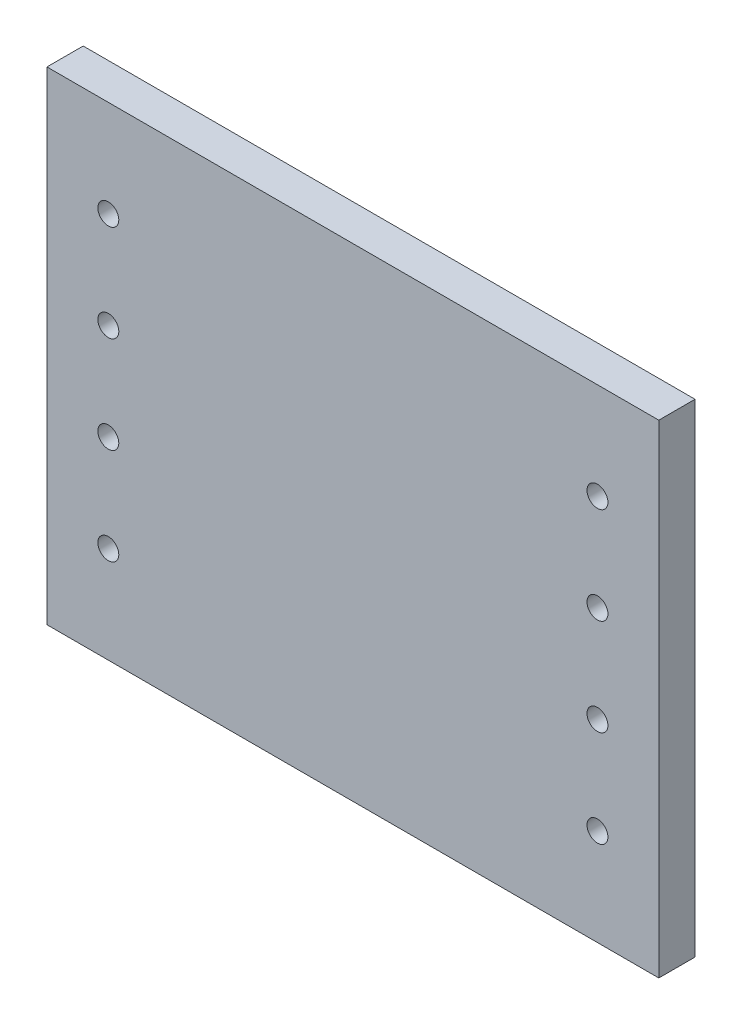
SolidWorks part; units mm, degrees
ref_plane "Front" through (0, 0, 0) normal (0, 0, 1) x (1, 0, 0)
ref_plane "Top" through (0, 0, 0) normal (0, 1, 0) x (1, 0, 0)
ref_plane "Right" through (0, 0, 0) normal (1, 0, 0) x (0, 0, -1)
sketch "Sketch1" plane through (0, 0, 0) normal (0, 0, 1) x (1, 0, 0)
  line L1 (23.481, 212.5625) -> (345.172, 212.5625)
  line L2 (345.172, 441.1625) -> (345.172, 237.9625) construction
  line L3 (23.481, 466.5625) -> (345.172, 466.5625)
  line L4 (345.172, 212.5625) -> (345.172, 466.5625)
  line L5 (345.172, 441.1625) -> (345.172, 237.9625) construction
  line L6 (23.481, 466.5625) -> (23.481, 212.5625)
  dimension "D2" = 254
extrude "Base-Extrude" add sketch "Sketch1" along normal blind 19.05
sketch "Sketch2" plane through (0, 0, 0) normal (0, 0, -1) x (-1, 0, 0)
  line L1 (-345.172, 466.5625) -> (-23.481, 466.5625) construction
  line L2 (-345.172, 466.5625) -> (-23.481, 466.5625) construction
  line L3 (-273.2265, 392.2739) -> (-273.2265, 245.7761)
  line L4 (-23.481, 212.5625) -> (-345.172, 212.5625) construction
  line L5 (-105.1421, 403.0625) -> (-263.511, 403.0625)
  line L6 (-105.1421, 403.0625) -> (-95.4265, 392.2739)
  line L7 (-263.511, 403.0625) -> (-273.2265, 392.2739)
  line L8 (-273.2265, 245.7761) -> (-95.4265, 245.7761)
  line L9 (-95.4265, 392.2739) -> (-95.4265, 245.7761)
  line L10 (-23.481, 212.5625) -> (-345.172, 212.5625) construction
  line L11 (-184.3265, 466.5625) -> (-184.3265, 212.5625) construction
  dimension "D1" = 177.8
extrude "Boss-Extrude1" add sketch "Sketch2" along normal blind 15.875
sketch "Sketch3" plane through (0, 0, -15.875) normal (0, 0, -1) x (-1, 0, 0)
  line L24 (-254.1765, 264.8261) -> (-114.4765, 264.8261)
  line L25 (-114.4765, 264.8261) -> (-114.4765, 384.0125)
  line L26 (-114.4765, 384.0125) -> (-254.1765, 384.0125)
  line L27 (-254.1765, 384.0125) -> (-254.1765, 264.8261)
  line L28 (-254.1765, 264.8261) -> (-114.4765, 264.8261)
  line L29 (-114.4765, 264.8261) -> (-114.4765, 384.0125)
  line L30 (-114.4765, 384.0125) -> (-254.1765, 384.0125)
  line L31 (-254.1765, 384.0125) -> (-254.1765, 264.8261)
  dimension "D2" = 19.05
extrude "Cut-Extrude1" cut sketch "Sketch3" against normal up to surface (15.875 mm away) up to face at (184.3265, 339.5625, 0)
fillet "Fillet3" radius 2.54 6 edges at (95.4265, 319.025, 0) (100.2843, 397.6682, 0) (184.3265, 403.0625, 0) (268.3688, 397.6682, 0) (273.2265, 319.025, 0) (184.3265, 245.7761, 0)
fillet "Fillet5" radius 6.35 4 edges at (254.1765, 264.8261, -7.9375) (114.4765, 264.8261, -7.9375) (114.4765, 384.0125, -7.9375) (254.1765, 384.0125, -7.9375)
fillet "Fillet6" radius 2.54 8 edges at (254.1765, 324.4193, 0) (184.3265, 384.0125, 0) (184.3265, 264.8261, 0) (114.4765, 324.4193, 0) (116.3364, 266.686, 0) (116.3364, 382.1526, 0) (252.3167, 266.686, 0) (252.3167, 382.1526, 0)
hole_wizard "CBORE for M10 SHCS1" positions "Sketch7" profile "Sketch6" counterbore size "M10" standard "Ansi Metric" end condition through all
sketch "Sketch7" plane through (0, 0, 0) normal (0, 0, -1) x (-1, 0, 0)
  line L0 (-345.172, 212.5625) -> (-345.172, 466.5625) construction
  line L1 (-345.172, 466.5625) -> (-23.481, 466.5625) construction
  point P0 (-312.914, 415.7625)
  dimension "D1" = 32.258
  dimension "D2" = 50.8
sketch "Sketch6" plane through (312.914, 415.7625, 0) normal (1, 0, 0) x (0, 1, 0)
  line L0 (0, 0) -> (0, 19.05)
  line L1 (0, 19.05) -> (5.5, 19.05)
  line L3 (5.5, 19.05) -> (5.5, 10)
  line L4 (5.5, 10) -> (9, 10)
  line L5 (9, 10) -> (9, 0)
  line L7 (9, 0) -> (0, 0)
  line L11 (0, -6.35) -> (0, 107.95) construction
  dimension "Thru Hole Dia." = 11
  dimension "Thru Hole Depth" = 19.05
  dimension "C'Bore Dia." = 18
  dimension "C'Bore Depth" = 10
pattern_linear "LPattern1" count 4 spacing 50.8 along (0, -1, 0) of "CBORE for M10 SHCS1"
hole_wizard "CBORE for M10 SHCS2" positions "Sketch9" profile "Sketch8" counterbore size "M10" standard "Ansi Metric" end condition through all
sketch "Sketch9" plane through (0, 0, 0) normal (0, 0, -1) x (-1, 0, 0)
  line L0 (-23.481, 466.5625) -> (-23.481, 212.5625) construction
  line L1 (-345.172, 466.5625) -> (-23.481, 466.5625) construction
  point P0 (-55.739, 415.7625)
  dimension "D1" = 32.258
  dimension "D2" = 50.8
sketch "Sketch8" plane through (55.739, 415.7625, 0) normal (1, 0, 0) x (0, 1, 0)
  line L0 (0, 0) -> (0, 19.05)
  line L1 (0, 19.05) -> (5.5, 19.05)
  line L3 (5.5, 19.05) -> (5.5, 10)
  line L4 (5.5, 10) -> (9, 10)
  line L5 (9, 10) -> (9, 0)
  line L7 (9, 0) -> (0, 0)
  line L11 (0, -6.35) -> (0, 107.95) construction
  dimension "Thru Hole Dia." = 11
  dimension "Thru Hole Depth" = 19.05
  dimension "C'Bore Dia." = 18
  dimension "C'Bore Depth" = 10
pattern_linear "LPattern2" count 4 spacing 50.8 along (0, -1, 0) of "CBORE for M10 SHCS2"
